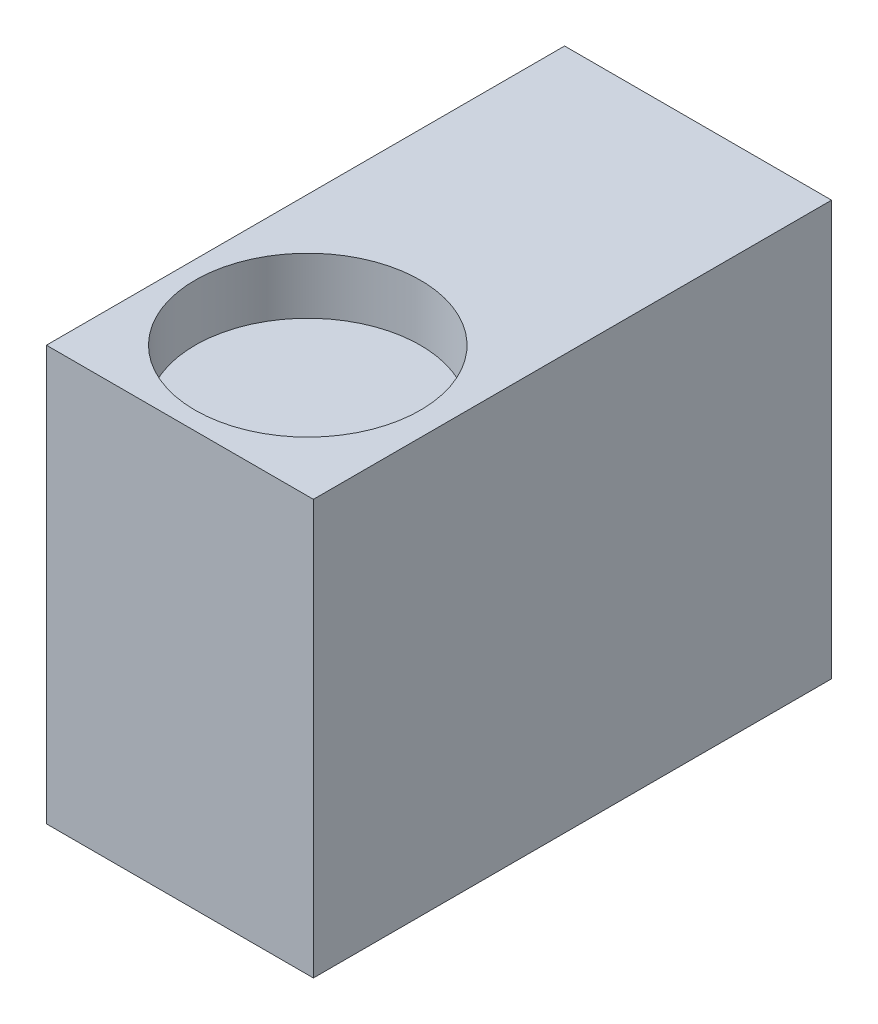
SolidWorks part; units mm, degrees
ref_plane "Front Plane" through (0, 0, 0) normal (0, 0, 1) x (1, 0, 0)
ref_plane "Top Plane" through (0, 0, 0) normal (0, 1, 0) x (1, 0, 0)
ref_plane "Right Plane" through (0, 0, 0) normal (1, 0, 0) x (0, 0, -1)
sketch "Sketch1" plane through (0, 0, 0) normal (0, 0, 1) x (1, 0, 0)
  line L1 (-14.6079, 14.1814) -> (9.0921, 14.1814)
  line L2 (-14.6079, 14.1814) -> (-14.6079, -22.6186)
  line L3 (-14.6079, -22.6186) -> (9.0921, -22.6186)
  line L4 (9.0921, 14.1814) -> (9.0921, -22.6186)
  dimension "D1" = 36.8
  dimension "D2" = 23.7
extrude "Boss-Extrude2" add sketch "Sketch1" along normal blind 46
sketch "Sketch2" plane through (0, 14.1814, 0) normal (0, 1, 0) x (1, 0, 0)
  circle A0 centre (-3.0079, -34.4) radius 11.6
  circle A1 centre (-3.0079, -34.4) radius 10
  point P3 (-1.4011, -28.9481)
extrude "Cut-Extrude1" cut sketch "Sketch2" against normal blind 5 contours A1
ref_plane "Plane1" through (0, -4.2186, 0) normal (0, 1, 0) x (1, 0, 0)
mirror "Mirror1" about plane through (0, -4.2186, 0) normal (0, 1, 0) of "Cut-Extrude1"
